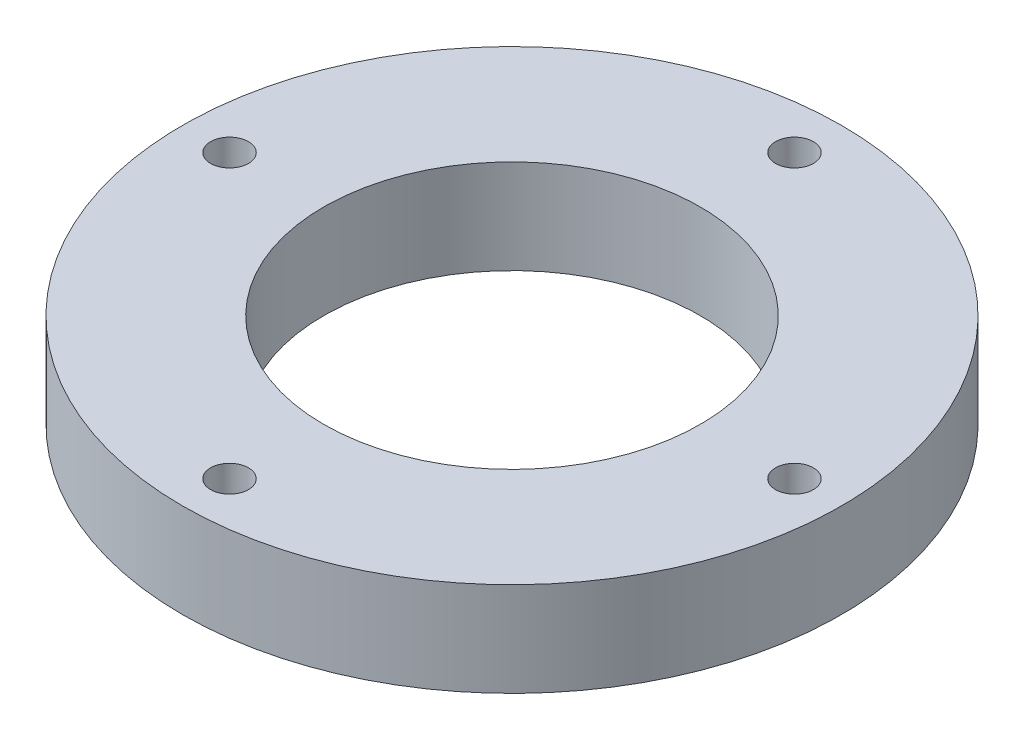
SolidWorks part; units mm, degrees
ref_plane "Front Plane" through (0, 0, 0) normal (0, 0, 1) x (1, 0, 0)
ref_plane "Top Plane" through (0, 0, 0) normal (0, 1, 0) x (1, 0, 0)
ref_plane "Right Plane" through (0, 0, 0) normal (1, 0, 0) x (0, 0, -1)
sketch "Sketch1" plane through (0, 0, 0) normal (0, 1, 0) x (1, 0, 0)
  circle A0 centre (0, 0) radius 44.45
  dimension "D1" = 88.9
extrude "Boss-Extrude1" add sketch "Sketch1" along normal blind 12.7
sketch "Sketch2" plane through (0, 12.7, 0) normal (0, 1, 0) x (1, 0, 0)
  circle A0 centre (0, 0) radius 25.4
  dimension "D1" = 50.8
extrude "Cut-Extrude1" cut sketch "Sketch2" against normal through all
hole_wizard "#7 (0.201) Diameter Hole1" positions "Sketch4" profile "Sketch3" hole size "#7" standard "Ansi Inch" end condition through all
sketch "Sketch4" plane through (0, 12.7, 0) normal (0, 1, 0) x (-1, 0, 0)
  point P0 (0, -38.1)
  dimension "D1" = 38.1
sketch "Sketch3" plane through (0, 12.7, -38.1) normal (1, 0, 0) x (0, 0, 1)
  line L0 (0, 0) -> (0, 12.7)
  line L1 (0, 12.7) -> (2.5527, 12.7)
  line L2 (2.5527, 12.7) -> (2.5527, 0)
  line L5 (2.5527, 0) -> (0, 0)
  line L11 (0, -6.35) -> (0, 107.95) construction
  dimension "Thru Hole Dia." = 5.1054
  dimension "Thru Hole Depth" = 12.7
pattern_circular "CirPattern1" count 4 over 360 about axis through (0, 0, 0) along (0, 1, 0) of "#7 (0.201) Diameter Hole1"
